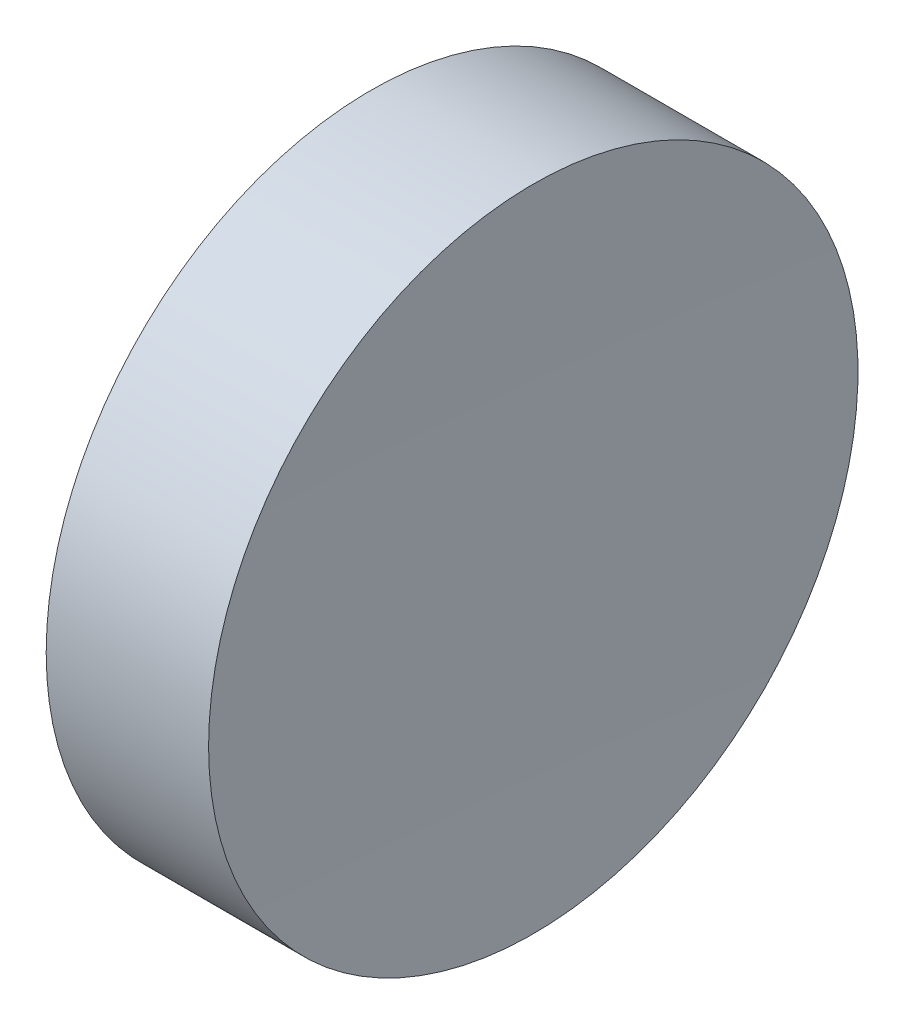
SolidWorks part; units mm, degrees
ref_plane "前视基准面" through (0, 0, 0) normal (0, 0, 1) x (1, 0, 0)
ref_plane "上视基准面" through (0, 0, 0) normal (0, 1, 0) x (1, 0, 0)
ref_plane "右视基准面" through (0, 0, 0) normal (1, 0, 0) x (0, 0, -1)
sketch "草图1" plane through (0, 0, 0) normal (0, 1, 0) x (1, 0, 0)
  line L0 (0, 0) -> (6.9328, 0) construction
  line L1 (0, 0) -> (6.19, 0)
  line L2 (0, 0) -> (0, 12.7)
  line L3 (0, 12.7) -> (6.3513, 12.7)
  arc A0 (6.3513, 12.7) -> (6.19, 0) centre (506.19, 0) ccw
  dimension "D3" = 500
  dimension "D1" = 6.19
  dimension "D2" = 12.7
revolve "旋转1" add sketch "草图1" angle 360 about L0
